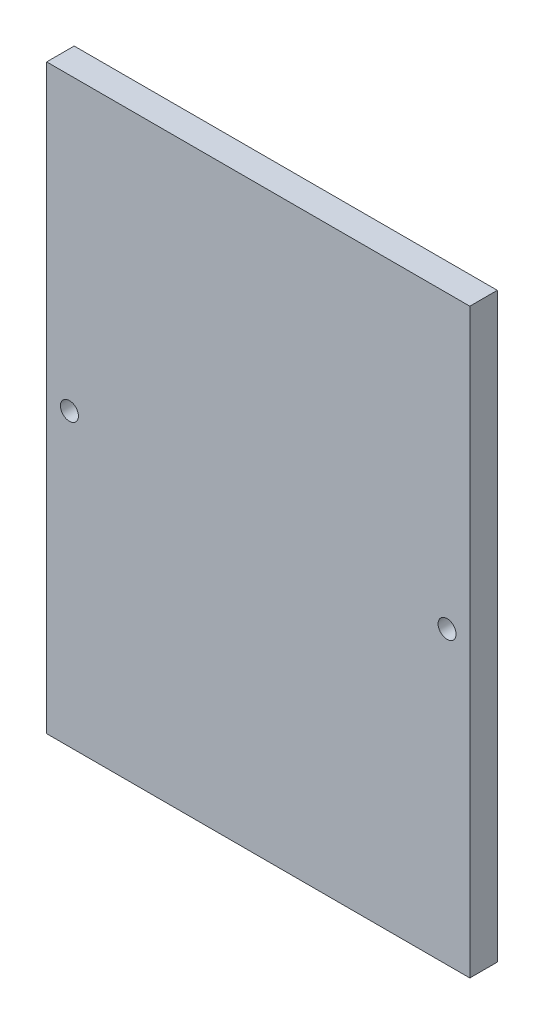
SolidWorks part; units mm, degrees
material "Acrylic (Medium-high impact)"
ref_plane "Front Plane" through (0, 0, 0) normal (0, 0, 1) x (1, 0, 0)
ref_plane "Top Plane" through (0, 0, 0) normal (0, 1, 0) x (1, 0, 0)
ref_plane "Right Plane" through (0, 0, 0) normal (1, 0, 0) x (0, 0, -1)
sketch "Sketch1" plane through (0, 0, 0) normal (0, 0, 1) x (1, 0, 0)
  line L1 (-94.5483, 65.5085) -> (-43.7483, 65.5085)
  line L2 (-94.5483, 65.5085) -> (-94.5483, -4.3415)
  line L3 (-94.5483, -4.3415) -> (-43.7483, -4.3415)
  line L4 (-43.7483, 65.5085) -> (-43.7483, -4.3415)
  point P0 (-69.1483, 30.5835)
  dimension "D1" = 69.85
  dimension "D2" = 50.8
extrude "Boss-Extrude2" add sketch "Sketch1" along normal blind 3.302 contours L1 L4 L3 L2
sketch "Sketch2" plane through (0, 0, 3.302) normal (0, 0, 1) x (1, 0, 0)
  line L0 (-94.5483, 65.5085) -> (-43.7483, 65.5085) construction
  line L1 (-43.7483, 65.5085) -> (-43.7483, -4.3415) construction
  line L2 (-94.5483, -4.3415) -> (-43.7483, -4.3415) construction
  line L3 (-94.5483, 65.5085) -> (-94.5483, -4.3415) construction
  circle A0 centre (-46.4788, 30.5835) radius 1.0795
  circle A1 centre (-91.8178, 30.5835) radius 1.0795
  point P8 (-69.1483, -4.3415)
  dimension "D1" = 2.159
  dimension "D2" = 2.159
  dimension "D3" = 34.925
  dimension "D4" = 2.7305
  dimension "D5" = 34.925
  dimension "D6" = 2.7305
extrude "Cut-Extrude1" cut sketch "Sketch2" against normal through all
